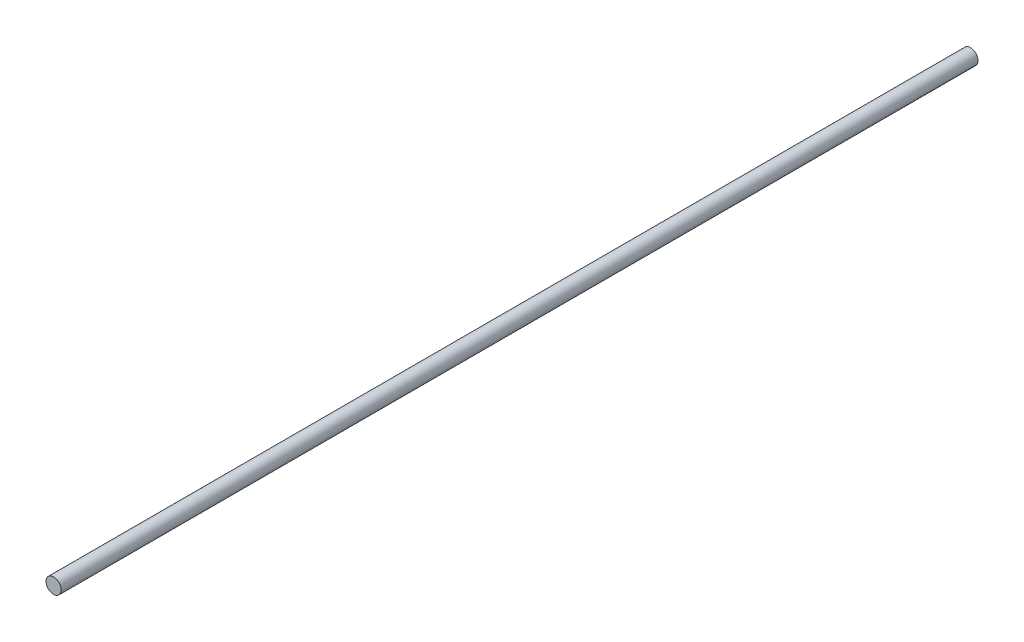
SolidWorks part; units mm, degrees
material "Bamboo"
ref_plane "Front Plane" through (0, 0, 0) normal (0, 0, 1) x (1, 0, 0)
ref_plane "Top Plane" through (0, 0, 0) normal (0, 1, 0) x (1, 0, 0)
ref_plane "Right Plane" through (0, 0, 0) normal (1, 0, 0) x (0, 0, -1)
sketch "Sketch1" plane through (0, 0, 0) normal (0, 0, 1) x (1, 0, 0)
  circle A0 centre (0, 0) radius 0.1
  dimension "D1" = 0.2
extrude "Boss-Extrude1" add sketch "Sketch1" along normal blind 12.1
